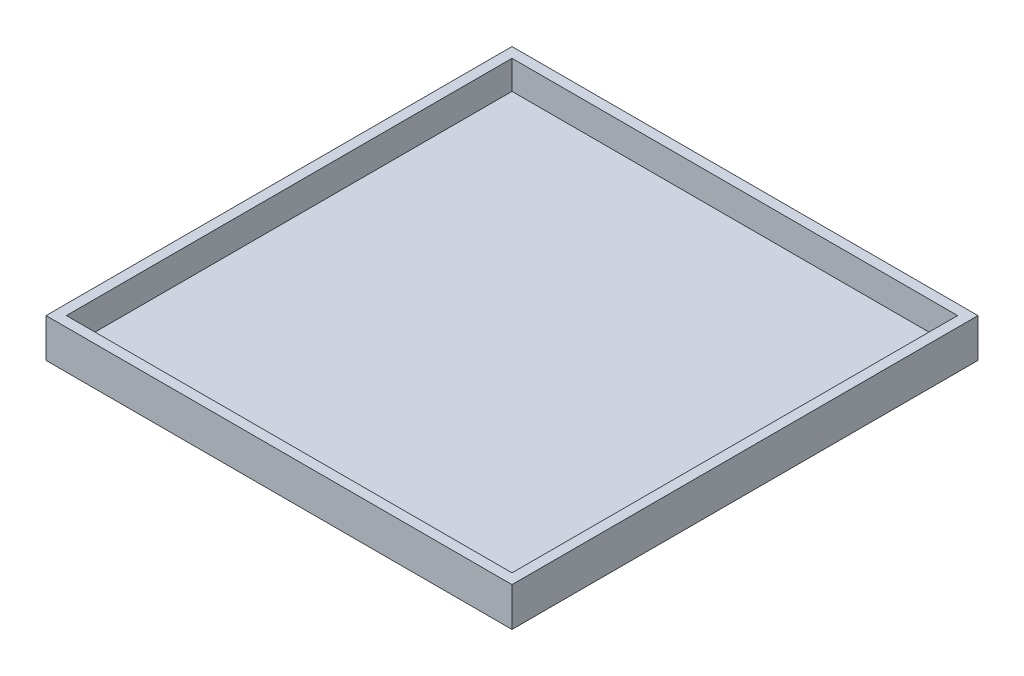
SolidWorks part; units mm, degrees
ref_plane "Front Plane" through (0, 0, 0) normal (0, 0, 1) x (1, 0, 0)
ref_plane "Top Plane" through (0, 0, 0) normal (0, 1, 0) x (1, 0, 0)
ref_plane "Right Plane" through (0, 0, 0) normal (1, 0, 0) x (0, 0, -1)
sketch "Sketch2" plane through (0, 0, 0) normal (0, 1, 0) x (1, 0, 0)
  line L1 (114.3, 114.3) -> (-114.3, 114.3)
  line L2 (114.3, 114.3) -> (114.3, -114.3)
  line L3 (114.3, -114.3) -> (-114.3, -114.3)
  line L4 (-114.3, 114.3) -> (-114.3, -114.3)
  line L5 (114.3, 114.3) -> (-114.3, -114.3) construction
  line L6 (114.3, -114.3) -> (-114.3, 114.3) construction
  point P0 (0, 0)
  dimension "D1" = 228.6
  dimension "D2" = 228.6
extrude "Boss-Extrude1" add sketch "Sketch2" along normal blind 19.05
shell "Shell1" thickness 5
sketch "Sketch4" plane through (0, 0, 0) normal (0, -1, 0) x (1, 0, 0)
  line L0 (73.66, -73.66) -> (73.66, 73.66)
  line L1 (76.2, -76.2) -> (-76.2, -76.2)
  line L2 (76.2, -76.2) -> (76.2, 76.2)
  line L3 (76.2, 76.2) -> (-76.2, 76.2)
  line L4 (-76.2, -76.2) -> (-76.2, 76.2)
  line L5 (76.2, -76.2) -> (-76.2, 76.2) construction
  line L6 (76.2, 76.2) -> (-76.2, -76.2) construction
  line L7 (73.66, 73.66) -> (-73.66, 73.66)
  line L8 (-73.66, -73.66) -> (-73.66, 73.66)
  line L9 (73.66, -73.66) -> (-73.66, -73.66)
  point P0 (0, 0)
  dimension "D1" = 152.4
  dimension "D2" = 152.4
  dimension "D3" = 2.54
extrude "Cut-Extrude1" cut sketch "Sketch4" against normal blind 2.54
sketch "Sketch6" plane through (0, 0, 0) normal (0, -1, 0) x (1, 0, 0)
  line L0 (-73.66, -8.5413) -> (73.66, -8.5413) construction
  line L1 (-73.66, 73.66) -> (-73.66, -73.66) construction
  line L2 (73.66, -73.66) -> (73.66, 73.66) construction
  text T0 "  Bb" font "Century Gothic" height in points 175
extrude "Cut-Extrude2" cut sketch "Sketch6" against normal blind 2.54
sketch "Sketch7" plane through (0, 0, 0) normal (0, -1, 0) x (1, 0, 0)
  line L0 (-73.66, -36.1209) -> (73.66, -36.1209) construction
  line L1 (-73.66, 73.66) -> (-73.66, -73.66) construction
  line L2 (73.66, -73.66) -> (73.66, 73.66) construction
  line L3 (-73.66, -25.9171) -> (73.66, -25.9171) construction
  line L4 (-73.66, 73.66) -> (-73.66, -73.66) construction
  text T0 "   BrewBuddy" font "Century Gothic" height in points 60
extrude "Cut-Extrude3" cut sketch "Sketch7" against normal blind 2.54
sketch "Sketch8" plane through (0, 0, 0) normal (0, -1, 0) x (1, 0, 0)
  line L0 (-73.66, -42.5684) -> (73.66, -42.5684) construction
  line L1 (-73.66, 73.66) -> (-73.66, -73.66) construction
  line L2 (73.66, -73.66) -> (73.66, 73.66) construction
  text T0 "        04.2025" font "Century Gothic" height in points 50
extrude "Cut-Extrude4" cut sketch "Sketch8" against normal blind 2.54
sketch "Sketch9" plane through (0, 0, 0) normal (0, -1, 0) x (-1, 0, 0)
  line L0 (73.66, -53.3367) -> (-73.66, -53.3367) construction
  line L1 (73.66, -73.66) -> (73.66, 73.66) construction
  line L2 (-73.66, 73.66) -> (-73.66, -73.66) construction
  line L3 (73.66, -56.9307) -> (-73.66, -56.9307) construction
  text T0 " 2" font "Century Gothic" height in points 50
extrude "Cut-Extrude5" cut sketch "Sketch9" against normal blind 2.54
